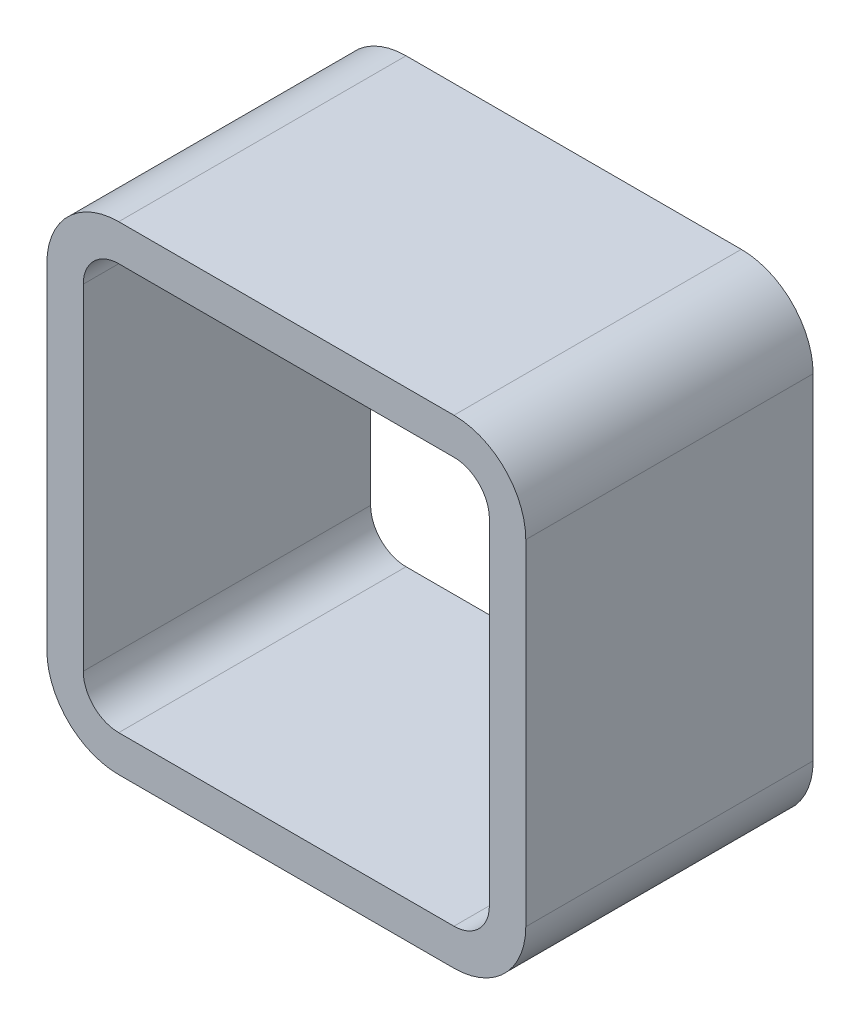
SolidWorks part; units mm, degrees
material "ASTM A36 Steel"
ref_plane "Front Plane" through (0, 0, 0) normal (0, 0, 1) x (1, 0, 0)
ref_plane "Top Plane" through (0, 0, 0) normal (0, 1, 0) x (1, 0, 0)
ref_plane "Right Plane" through (0, 0, 0) normal (1, 0, 0) x (0, 0, -1)
sketch "Sketch1" plane through (0, 0, 0) normal (0, 0, 1) x (1, 0, 0)
  line L0 (-11.1125, 15.875) -> (11.1125, 15.875)
  line L1 (15.875, 11.1125) -> (15.875, -11.1125)
  line L2 (11.1125, -15.875) -> (-11.1125, -15.875)
  line L3 (-15.875, -11.1125) -> (-15.875, 11.1125)
  line L4 (0, 15.875) -> (0, -15.875) construction
  line L5 (-15.875, 0) -> (15.875, 0) construction
  line L6 (-11.1125, 13.462) -> (11.1125, 13.462)
  line L7 (13.462, 11.1125) -> (13.462, -11.1125)
  line L8 (11.1125, -13.462) -> (-11.1125, -13.462)
  line L9 (-13.462, -11.1125) -> (-13.462, 11.1125)
  arc A0 (11.1125, 15.875) -> (15.875, 11.1125) centre (11.1125, 11.1125) cw
  arc A1 (15.875, -11.1125) -> (11.1125, -15.875) centre (11.1125, -11.1125) cw
  arc A2 (-11.1125, -15.875) -> (-15.875, -11.1125) centre (-11.1125, -11.1125) cw
  arc A3 (-15.875, 11.1125) -> (-11.1125, 15.875) centre (-11.1125, 11.1125) cw
  arc A4 (11.1125, 13.462) -> (13.462, 11.1125) centre (11.1125, 11.1125) cw
  arc A5 (13.462, -11.1125) -> (11.1125, -13.462) centre (11.1125, -11.1125) cw
  arc A6 (-11.1125, -13.462) -> (-13.462, -11.1125) centre (-11.1125, -11.1125) cw
  arc A7 (-13.462, 11.1125) -> (-11.1125, 13.462) centre (-11.1125, 11.1125) cw
  point P16 (0, 0)
  dimension "D2" = 4.7625
  dimension "D1" = 31.75
  dimension "D3" = 2.413
extrude "Boss-Extrude1" add sketch "Sketch1" along normal blind 19.05
